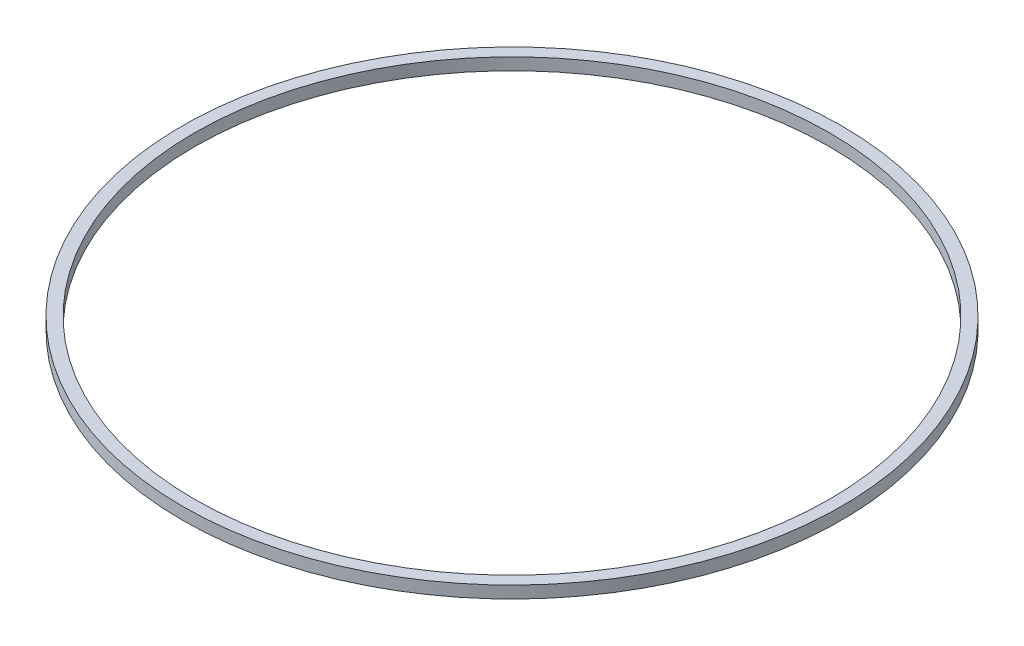
SolidWorks part; units mm, degrees
ref_plane "Front Plane" through (0, 0, 0) normal (0, 0, 1) x (1, 0, 0)
ref_plane "Top Plane" through (0, 0, 0) normal (0, 1, 0) x (1, 0, 0)
ref_plane "Right Plane" through (0, 0, 0) normal (1, 0, 0) x (0, 0, -1)
sketch "Sketch1" plane through (0, 0, 0) normal (0, 0, 1) x (1, 0, 0)
  line L0 (0, 0) -> (0, 45.855) construction
  line L1 (2000, 38.1) -> (2076.2, 38.1)
  line L2 (2000, 38.1) -> (2000, -38.1)
  line L3 (2000, -38.1) -> (2076.2, -38.1)
  line L4 (2076.2, 38.1) -> (2076.2, -38.1)
  line L5 (2000, 38.1) -> (2076.2, -38.1) construction
  line L6 (2000, -38.1) -> (2076.2, 38.1) construction
  point P0 (2038.1, 0)
  point P5 (2000, 0)
  dimension "D1" = 2000
  dimension "D2" = 76.2
  dimension "D3" = 76.2
revolve "Revolve1" add sketch "Sketch1" angle 360 about L0
